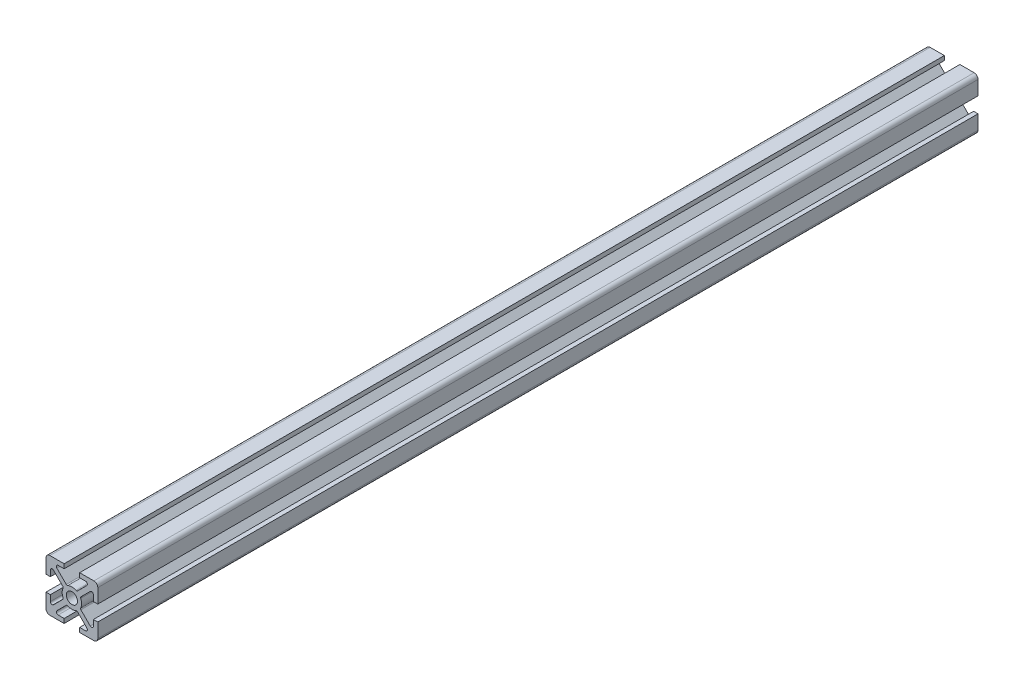
SolidWorks part; units mm, degrees
material "6063-T5"
ref_plane "Face" through (0, 0, 0) normal (0, 0, 1) x (1, 0, 0)
ref_plane "Dessus" through (0, 0, 0) normal (0, 1, 0) x (1, 0, 0)
ref_plane "Droite" through (0, 0, 0) normal (1, 0, 0) x (0, 0, -1)
sketch "Esquisse1" plane through (0, 0, 0) normal (0, 0, 1) x (1, 0, 0)
  line L0 (-3, 10) -> (-8.5, 10)
  line L2 (-3, -10) -> (-3, -8.3)
  line L3 (-3, -8.3) -> (-5.2994, -8.3)
  line L4 (-5.7944, -7.105) -> (-2.1755, -3.4861)
  line L6 (2.1755, -3.4861) -> (5.7944, -7.105)
  line L7 (5.2994, -8.3) -> (3, -8.3)
  line L8 (3, -8.3) -> (3, -10)
  line L11 (3, -10) -> (8.5, -10)
  line L12 (10, -8.5) -> (10, -3)
  line L15 (10, -3) -> (8.3, -3)
  line L16 (8.3, -3) -> (8.3, -5.2994)
  line L17 (7.105, -5.7944) -> (3.4861, -2.1755)
  line L20 (3.4861, 2.1755) -> (7.105, 5.7944)
  line L21 (8.3, 5.2994) -> (8.3, 3)
  line L22 (8.3, 3) -> (10, 3)
  line L25 (10, 3) -> (10, 8.5)
  line L26 (8.5, 10) -> (3.5, 10)
  line L29 (3, 10) -> (3, 8.3)
  line L30 (3, 8.3) -> (5.2994, 8.3)
  line L31 (5.7944, 7.105) -> (2.1755, 3.4861)
  line L34 (-2.1755, 3.4861) -> (-5.7944, 7.105)
  line L35 (-5.2994, 8.3) -> (-3, 8.3)
  line L36 (-3, 8.3) -> (-3, 10)
  line L39 (3.5, 10) -> (3, 10)
  line L40 (-10, 8.5) -> (-10, 3)
  line L43 (-10, 3) -> (-8.3, 3)
  line L44 (-8.3, 3) -> (-8.3, 5.2994)
  line L45 (-7.105, 5.7944) -> (-3.4861, 2.1755)
  line L48 (-3.4861, -2.1755) -> (-7.105, -5.7944)
  line L49 (-8.3, -5.2994) -> (-8.3, -3)
  line L50 (-8.3, -3) -> (-10, -3)
  line L53 (-10, -3) -> (-10, -8.5)
  line L54 (-8.5, -10) -> (-3, -10)
  line L55 (13.1941, 0) -> (-16.3684, 0) construction
  line L56 (0, 3.75) -> (0, -15.1011) construction
  line L58 (5.7944, 5.7944) -> (-5.2994, -5.2994) construction
  line L59 (5.7944, -5.7944) -> (-5.4107, 5.4107) construction
  circle A0 centre (0, 0) radius 2.15
  arc A1 (-5.2994, -8.3) -> (-5.7944, -7.105) centre (-5.2994, -7.6) cw
  arc A2 (-2.1755, -3.4861) -> (-1.6076, -3.388) centre (-1.8219, -3.8397) cw
  arc A3 (-1.6076, -3.388) -> (1.6076, -3.388) centre (0, 0) ccw
  arc A5 (1.6076, -3.388) -> (2.1755, -3.4861) centre (1.8219, -3.8397) cw
  arc A6 (5.7944, -7.105) -> (5.2994, -8.3) centre (5.2994, -7.6) cw
  arc A7 (8.5, -10) -> (10, -8.5) centre (8.5, -8.5) ccw
  arc A8 (8.3, -5.2994) -> (7.105, -5.7944) centre (7.6, -5.2994) cw
  arc A9 (3.4861, -2.1755) -> (3.388, -1.6076) centre (3.8397, -1.8219) cw
  arc A10 (3.388, -1.6076) -> (3.75, 0) centre (0, 0) ccw
  arc A11 (3.75, 0) -> (3.388, 1.6076) centre (0, 0) ccw
  arc A12 (3.388, 1.6076) -> (3.4861, 2.1755) centre (3.8397, 1.8219) cw
  arc A13 (7.105, 5.7944) -> (8.3, 5.2994) centre (7.6, 5.2994) cw
  arc A14 (10, 8.5) -> (8.5, 10) centre (8.5, 8.5) ccw
  arc A15 (5.2994, 8.3) -> (5.7944, 7.105) centre (5.2994, 7.6) cw
  arc A16 (2.1755, 3.4861) -> (1.6076, 3.388) centre (1.8219, 3.8397) cw
  arc A17 (1.6076, 3.388) -> (-1.6076, 3.388) centre (0, 0) ccw
  arc A19 (-1.6076, 3.388) -> (-2.1755, 3.4861) centre (-1.8219, 3.8397) cw
  arc A20 (-5.7944, 7.105) -> (-5.2994, 8.3) centre (-5.2994, 7.6) cw
  arc A21 (-8.5, 10) -> (-10, 8.5) centre (-8.5, 8.5) ccw
  arc A22 (-8.3, 5.2994) -> (-7.105, 5.7944) centre (-7.6, 5.2994) cw
  arc A23 (-3.4861, 2.1755) -> (-3.388, 1.6076) centre (-3.8397, 1.8219) cw
  arc A24 (-3.388, 1.6076) -> (-3.388, -1.6076) centre (0, 0) ccw
  arc A26 (-3.388, -1.6076) -> (-3.4861, -2.1755) centre (-3.8397, -1.8219) cw
  arc A27 (-7.105, -5.7944) -> (-8.3, -5.2994) centre (-7.6, -5.2994) cw
  arc A28 (-10, -8.5) -> (-8.5, -10) centre (-8.5, -8.5) ccw
  dimension "D3" = 4.3
  dimension "D4" = 1.5
  dimension "D15" = 0.7
  dimension "D19" = 3.75
  dimension "D20" = 0.5
  dimension "D1" = 20
  dimension "D2" = 20
  dimension "D10" = 10
  dimension "D11" = 10
  dimension "D12" = 3
  dimension "D13" = 3
  dimension "D16" = 1.7
  dimension "D17" = 5.2994
  dimension "D18" = 45
  dimension "D22" = 45
  dimension "D23" = 6
  dimension "D24" = 45
  dimension "D25" = 5.2994
  dimension "D26" = 45
extrude "Boss.-Extru.1" add sketch "Esquisse1" along normal blind 340
